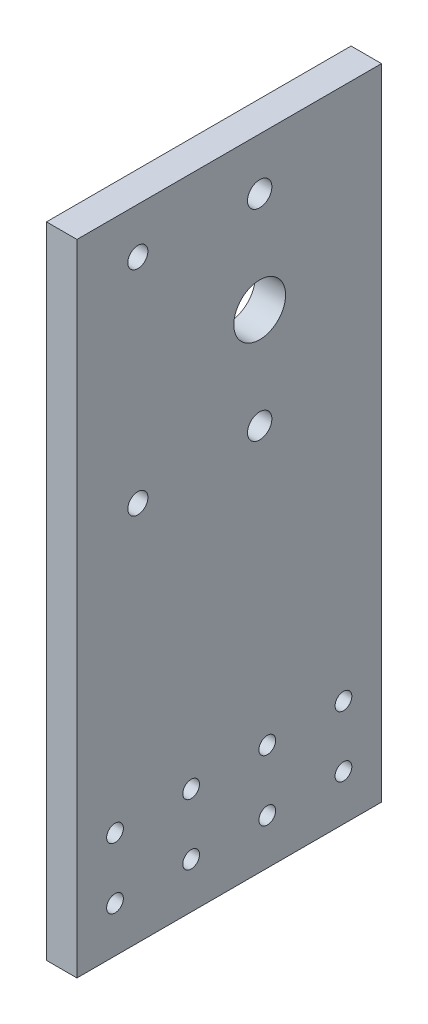
SolidWorks part; units mm, degrees
ref_plane "Front Plane" through (0, 0, 0) normal (0, 0, 1) x (1, 0, 0)
ref_plane "Top Plane" through (0, 0, 0) normal (0, 1, 0) x (1, 0, 0)
ref_plane "Right Plane" through (0, 0, 0) normal (1, 0, 0) x (0, 0, -1)
sketch "Sketch2" plane through (0, 0, 0) normal (1, 0, 0) x (0, 0, -1)
  line L0 (-60, 55) -> (40, 55) construction
  line L1 (40, -105) -> (-60, -105)
  line L2 (40, -105) -> (40, 105)
  line L3 (40, 105) -> (-60, 105)
  line L4 (-60, -105) -> (-60, 105)
  line L5 (40, -105) -> (-60, 105) construction
  line L6 (40, 105) -> (-60, -105) construction
  circle A0 centre (0, 88) radius 4
  circle A1 centre (0, 22) radius 4
  point P0 (0, 0)
  point P15 (-10, 0)
  dimension "D3" = 8
  dimension "D1" = 100
  dimension "D2" = 210
  dimension "D4" = 66
  dimension "D5" = 50
  dimension "D6" = 10
extrude "Boss-Extrude1" add sketch "Sketch2" along normal blind 10
sketch "Sketch3" plane through (10, 0, 0) normal (1, 0, 0) x (0, 0, -1)
  line L0 (-10, -105) -> (-10, -55) construction
  line L3 (-60, -105) -> (40, -105) construction
  line L5 (-35, -105) -> (-35, -55) construction
  line L6 (-10, -80) -> (-35, -80) construction
  line L8 (-35, -80) -> (-60, -80) construction
  line L9 (-60, 105) -> (-60, -105) construction
  circle A17 centre (-22.5, -70) radius 2.5
  circle A18 centre (-47.5, -70) radius 2.5
  circle A19 centre (-47.5, -90) radius 2.5
  circle A20 centre (-22.5, -90) radius 2.5
  circle A21 centre (2.5, -90) radius 2.5
  circle A22 centre (27.5, -90) radius 2.5
  circle A23 centre (27.5, -70) radius 2.5
  circle A24 centre (2.5, -70) radius 2.5
  point P15 (-22.5, -80)
  dimension "D1" = 25
  dimension "D2" = 25
  dimension "D3" = 5
  dimension "D4" = 20
extrude "mount" cut sketch "Sketch3" against normal through all
sketch "Sketch7" plane through (10, 0, 0) normal (1, 0, 0) x (0, 0, -1)
  line L0 (40, 105) -> (-60, 105) construction
  line L1 (-60, 105) -> (-60, -105) construction
  line L2 (0, 55) -> (-60, 55) construction
  line L3 (0, 88) -> (0, 22) construction
  circle A0 centre (-40, 90) radius 2.5
  circle A1 centre (-40, 20) radius 2.5
  dimension "D3" = 5
  dimension "D1" = 15
  dimension "D2" = 20
extrude "support_profile_mount" cut sketch "Sketch7" against normal through all
sketch "Sketch5" plane through (10, 0, 0) normal (1, 0, 0) x (0, 0, -1)
  line L0 (-60, 55) -> (40, 55) construction
  line L1 (-60, 105) -> (-60, -105) construction
  line L2 (40, -105) -> (40, 105) construction
  circle A0 centre (0, 22) radius 4 construction
  circle A1 centre (0, 88) radius 4 construction
  circle A2 centre (0, 55) radius 8.5
  dimension "D1" = 17
extrude "bearing_mount" cut sketch "Sketch5" against normal through all
sketch "Sketch4" plane through (10, 0, 0) normal (1, 0, 0) x (0, 0, -1)
  line L0 (-60, 55) -> (40, 55) construction
  line L1 (-60, 105) -> (-60, -105) construction
  line L2 (40, -105) -> (40, 105) construction
  line L3 (0, 55) -> (0, 0) construction
  circle A0 centre (0, 88) radius 4 construction
  circle A1 centre (0, 22) radius 4 construction
  circle A2 centre (0, 55) radius 11
  circle A3 centre (-15.5, 70.5) radius 1.5
  circle A4 centre (15.5, 70.5) radius 1.5
  circle A5 centre (-15.5, 39.5) radius 1.5
  circle A6 centre (15.5, 39.5) radius 1.5
  dimension "D1" = 22
  dimension "D2" = 3
  dimension "D3" = 31
  dimension "D4" = 31
extrude "stepper_mount" [suppressed] cut sketch "Sketch4" against normal through all
sketch "Sketch6" [suppressed] plane through (0, 0, 0) normal (-1, 0, 0) x (0, 0, 1)
  line L0 (0, 71.0219) -> (0, 55) construction
  line L1 (0, 55) -> (-40, 55) construction
  line L2 (-40, -105) -> (-40, 105) construction
  circle A0 centre (-15.5, 70.5) radius 2.75
  circle A1 centre (15.5, 70.5) radius 2.75
  circle A2 centre (15.5, 39.5) radius 2.75
  circle A3 centre (-15.5, 39.5) radius 2.75
  dimension "D1" = 5.5
extrude "stepper_mount_countersink" [suppressed] cut sketch "Sketch6" against normal blind 3
hole_wizard "CSK for M6 socket countersunk head screw1" [suppressed] positions "Sketch8" profile "Sketch9" countersink size "M6" standard "DIN"
sketch "Sketch8" plane through (10, 0, 0) normal (1, 0, 0) x (0, 0, -1)
  point P0 (-40, 90)
  point P3 (-40, 20)
sketch "Sketch9" plane through (10, 90, 40) normal (0, 1, 0) x (0, 0, -1)
  line L0 (0, 0) -> (0, 16.9828)
  line L1 (0, 16.9828) -> (3.3, 15)
  line L2 (3.3, 15) -> (3.3, 3.555)
  line L3 (3.3, 3.555) -> (6.855, 0)
  line L5 (6.855, 0) -> (0, 0)
  line L6 (-3.3, 3.555) -> (-6.855, 0) construction
  line L10 (0, 16.9828) -> (-3.3, 15) construction
  line L11 (0, -6.35) -> (0, 107.95) construction
  dimension "Hole Dia." = 6.6
  dimension "Hole Depth" = 15
  dimension "Near C'Sink Dia." = 13.71
  dimension "Near C'Sink Angle" = 90
  dimension "Drill Angle" = 118
hole_wizard "CSK for M5 socket countersunk head screw1" [suppressed] positions "Sketch10" profile "Sketch11" countersink size "M5" standard "DIN"
sketch "Sketch10" plane through (10, 0, 0) normal (1, 0, 0) x (0, 0, -1)
  point P0 (-47.5, -70)
  point P3 (-47.5, -90)
  point P6 (-22.5, -70)
  point P9 (-22.5, -90)
  point P12 (2.5, -70)
  point P15 (2.5, -90)
  point P18 (27.5, -90)
  point P21 (27.5, -70)
sketch "Sketch11" plane through (10, -70, 47.5) normal (0, 1, 0) x (0, 0, -1)
  line L0 (0, 0) -> (0, 16.6524)
  line L1 (0, 16.6524) -> (2.75, 15)
  line L2 (2.75, 15) -> (2.75, 2.985)
  line L3 (2.75, 2.985) -> (5.735, 0)
  line L5 (5.735, 0) -> (0, 0)
  line L6 (-2.75, 2.985) -> (-5.735, 0) construction
  line L10 (0, 16.6524) -> (-2.75, 15) construction
  line L11 (0, -6.35) -> (0, 107.95) construction
  dimension "Hole Dia." = 5.5
  dimension "Hole Depth" = 15
  dimension "Near C'Sink Dia." = 11.47
  dimension "Near C'Sink Angle" = 90
  dimension "Drill Angle" = 118
hole_wizard "CSK for M3 socket countersunk head screw2" [suppressed] positions "Sketch14" profile "Sketch15" countersink size "M3" standard "DIN"
sketch "Sketch14" plane through (0, 0, 0) normal (-1, 0, 0) x (0, 0, 1)
  point P0 (-15.5, 70.5)
  point P3 (-15.5, 39.5)
  point P6 (15.5, 39.5)
  point P9 (15.5, 70.5)
sketch "Sketch15" plane through (0, 70.5, -15.5) normal (0, 1, 0) x (0, 0, 1)
  line L0 (0, 0) -> (0, 16.0215)
  line L1 (0, 16.0215) -> (1.7, 15)
  line L2 (1.7, 15) -> (1.7, 1.77)
  line L3 (1.7, 1.77) -> (3.47, 0)
  line L5 (3.47, 0) -> (0, 0)
  line L6 (-1.7, 1.77) -> (-3.47, 0) construction
  line L10 (0, 16.0215) -> (-1.7, 15) construction
  line L11 (0, -6.35) -> (0, 107.95) construction
  dimension "Hole Dia." = 3.4
  dimension "Hole Depth" = 15
  dimension "Near C'Sink Dia." = 6.94
  dimension "Near C'Sink Angle" = 90
  dimension "Drill Angle" = 118
hole_wizard "CSK for M6 socket countersunk head screw2" positions "Sketch16" profile "Sketch17" countersink size "M6" standard "DIN"
sketch "Sketch16" plane through (0, 0, 0) normal (-1, 0, 0) x (0, 0, 1)
  point P0 (40, 90)
  point P3 (40, 20)
sketch "Sketch17" plane through (0, 90, 40) normal (0, 1, 0) x (0, 0, 1)
  line L0 (0, 0) -> (0, 16.9828)
  line L1 (0, 16.9828) -> (3.3, 15)
  line L2 (3.3, 15) -> (3.3, 3.555)
  line L3 (3.3, 3.555) -> (6.855, 0)
  line L5 (6.855, 0) -> (0, 0)
  line L6 (-3.3, 3.555) -> (-6.855, 0) construction
  line L10 (0, 16.9828) -> (-3.3, 15) construction
  line L11 (0, -6.35) -> (0, 107.95) construction
  dimension "Hole Dia." = 6.6
  dimension "Hole Depth" = 15
  dimension "Near C'Sink Dia." = 13.71
  dimension "Near C'Sink Angle" = 90
  dimension "Drill Angle" = 118
hole_wizard "CSK for M5 socket countersunk head screw2" positions "Sketch18" profile "Sketch19" countersink size "M5" standard "DIN"
sketch "Sketch18" plane through (0, 0, 0) normal (-1, 0, 0) x (0, 0, 1)
  point P0 (-27.5, -70)
  point P3 (-2.5, -70)
  point P6 (22.5, -70)
  point P9 (47.5, -70)
  point P12 (47.5, -90)
  point P15 (22.5, -90)
  point P18 (-2.5, -90)
  point P21 (-27.5, -90)
sketch "Sketch19" plane through (0, -70, -27.5) normal (0, 1, 0) x (0, 0, 1)
  line L0 (0, 0) -> (0, 16.6524)
  line L1 (0, 16.6524) -> (2.75, 15)
  line L2 (2.75, 15) -> (2.75, 2.985)
  line L3 (2.75, 2.985) -> (5.735, 0)
  line L5 (5.735, 0) -> (0, 0)
  line L6 (-2.75, 2.985) -> (-5.735, 0) construction
  line L10 (0, 16.6524) -> (-2.75, 15) construction
  line L11 (0, -6.35) -> (0, 107.95) construction
  dimension "Hole Dia." = 5.5
  dimension "Hole Depth" = 15
  dimension "Near C'Sink Dia." = 11.47
  dimension "Near C'Sink Angle" = 90
  dimension "Drill Angle" = 118
